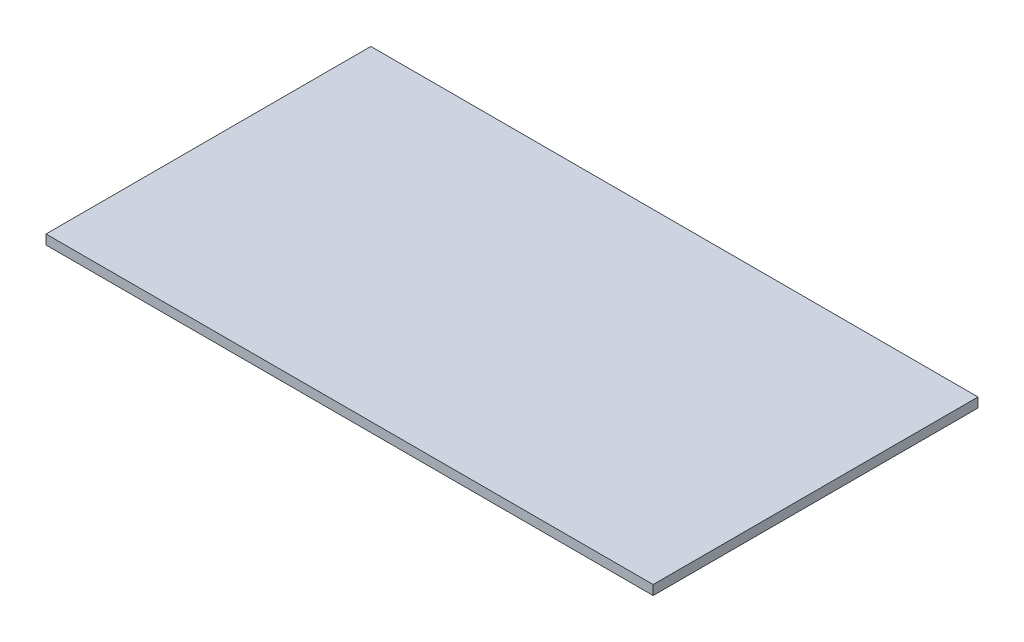
SolidWorks part; units mm, degrees
material "ABS"
ref_plane "Front Plane" through (0, 0, 0) normal (0, 0, 1) x (1, 0, 0)
ref_plane "Top Plane" through (0, 0, 0) normal (0, 1, 0) x (1, 0, 0)
ref_plane "Right Plane" through (0, 0, 0) normal (1, 0, 0) x (0, 0, -1)
sketch "Sketch1" plane through (0, 0, 0) normal (0, 1, 0) x (1, 0, 0)
  line L0 (7.898, 4.24) -> (0, 4.24)
  line L5 (0, -4.24) -> (0, 4.24) construction
  line L6 (0, 4.24) -> (-7.952, 4.24)
  line L7 (-7.952, 4.24) -> (-7.952, -4.24)
  line L8 (-7.952, -4.24) -> (7.898, -4.24)
  line L9 (7.898, -4.24) -> (7.898, 4.24)
  point P3 (0, 0)
  dimension "D1" = 8.48
  dimension "D2" = 15.85
  dimension "D3" = 7.952
extrude "Boss-Extrude1" add sketch "Sketch1" along normal blind 0.25
sketch "Sketch2"
